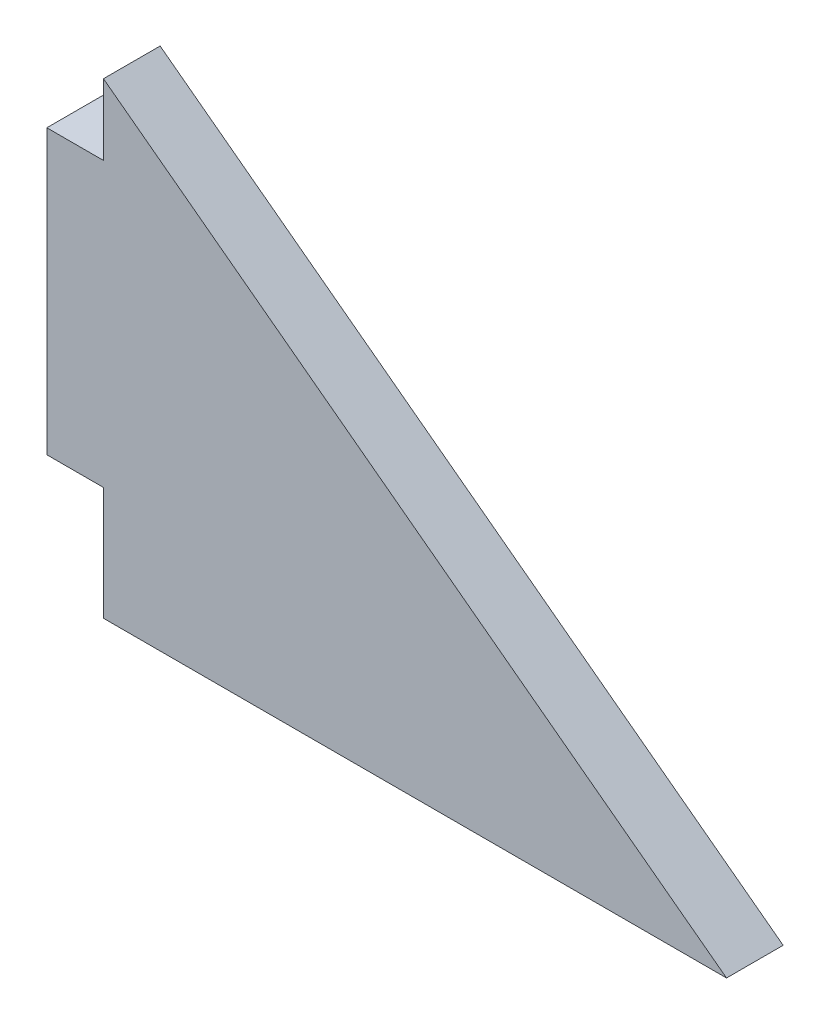
SolidWorks part; units mm, degrees
material "ﾊﾞﾙｻ"
ref_plane "正面" through (0, 0, 0) normal (0, 0, 1) x (1, 0, 0)
ref_plane "平面" through (0, 0, 0) normal (0, 1, 0) x (1, 0, 0)
ref_plane "右側面" through (0, 0, 0) normal (1, 0, 0) x (0, 0, -1)
sketch "ｽｹｯﾁ1" plane through (0, 0, 0) normal (0, 0, 1) x (1, 0, 0)
  line L0 (0, 0) -> (0, 10)
  line L1 (0, 10) -> (2, 10)
  line L2 (2, 10) -> (2, 12.5)
  line L3 (2, 12.5) -> (24, -4)
  line L4 (24, -4) -> (2, -4)
  line L5 (2, -4) -> (2, 0)
  line L6 (2, 0) -> (0, 0)
  point P8 (1, 0)
  point P9 (2.0641, 12.5992)
  dimension "D1" = 2
  dimension "D2" = 4
  dimension "D3" = 10
  dimension "D4" = 2.5
  dimension "D5" = 22
extrude "ﾎﾞｽ - 押し出し1" add sketch "ｽｹｯﾁ1" along normal blind 2
